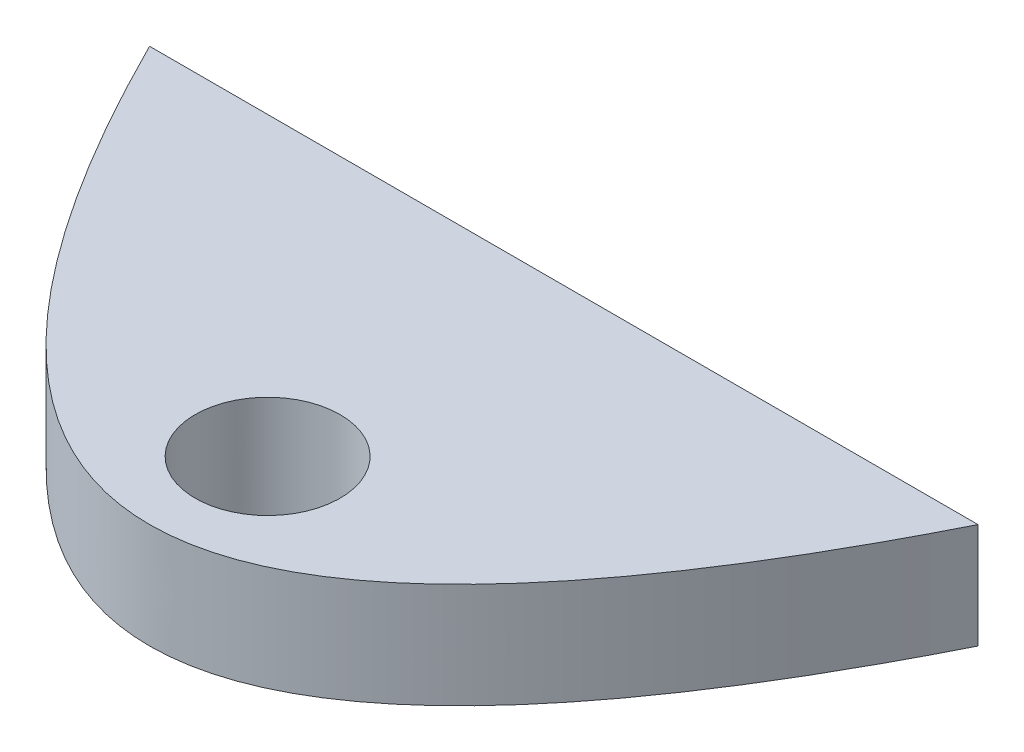
SolidWorks part; units mm, degrees
material "Custom Plastic (2)"
ref_plane "Front Plane" through (0, 0, 0) normal (0, 0, 1) x (1, 0, 0)
ref_plane "Top Plane" through (0, 0, 0) normal (0, 1, 0) x (1, 0, 0)
ref_plane "Right Plane" through (0, 0, 0) normal (1, 0, 0) x (0, 0, -1)
sketch "Sketch1" plane through (0, 0, 0) normal (0, 1, 0) x (1, 0, 0)
  line L0 (-200, 0) -> (200, 0)
  spline S0 degree 2 poles (-225.2396, 53.6645) (0, -453.6645) (225.2396, 53.6645) knots 0 0 0 1 1 1 construction
  spline S1 degree 2 poles (-200, 0) (0, -400) (200, 0) knots 0.056028 0.056028 0.056028 0.943972 0.943972 0.943972
extrude "Boss-Extrude1" add sketch "Sketch1" along normal blind 300
sketch "Sketch2" plane through (0, 300, 0) normal (0, 1, 0) x (1, 0, 0)
  line L0 (0, 200) -> (0, -200)
  line L2 (200, 0) -> (-200, 0) construction
  circle A0 centre (0, -143) radius 35
  parabola Q0 (-200, 0) -> (200, 0) focus (0, -150) apex (0, -200) construction
  point P4 (0, 0)
  dimension "D1" = 70
  dimension "D2" = 143
ref_plane "Plane1" through (0, 150, 0) normal (0, 1, 0) x (1, 0, 0)
sketch "Sketch3" plane through (0, 150, 0) normal (0, 1, 0) x (1, 0, 0)
  circle A0 centre (0, -143) radius 15.5
  dimension "D1" = 31
extrude "Cut-Extrude1" cut sketch "Sketch3" against normal blind 23 and the other way blind 23
ref_plane "Plane2" through (0, 173, 0) normal (0, 1, 0) x (1, 0, 0)
sketch "Sketch4" plane through (0, 173, 0) normal (0, 1, 0) x (1, 0, 0)
  circle A0 centre (0, -143) radius 35
extrude "Cut-Extrude3" cut sketch "Sketch4" along normal blind 300 contours A0
mirror "Mirror1" about plane through (0, 150, 0) normal (0, 1, 0) of "Cut-Extrude3"
sketch "Sketch5" plane through (0, 0, 0) normal (0, 0, -1) x (-1, 0, 0)
  line L0 (-200, 300) -> (200, 300) construction
  line L1 (-252.2562, 319.8805) -> (243.9695, 319.8805)
  line L2 (-252.2562, 319.8805) -> (-252.2562, 249.2)
  line L3 (-252.2562, 249.2) -> (243.9695, 249.2)
  line L4 (243.9695, 319.8805) -> (243.9695, 249.2)
  line L6 (-252.2562, 198.4) -> (252.2562, 198.4)
  line L7 (-252.2562, 198.4) -> (-252.2562, -39.9638)
  line L8 (-252.2562, -39.9638) -> (252.2562, -39.9638)
  line L9 (252.2562, 198.4) -> (252.2562, -39.9638)
  dimension "D1" = 50.8
  dimension "D2" = 50.8
extrude "Cut-Extrude4" cut sketch "Sketch5" against normal through all
